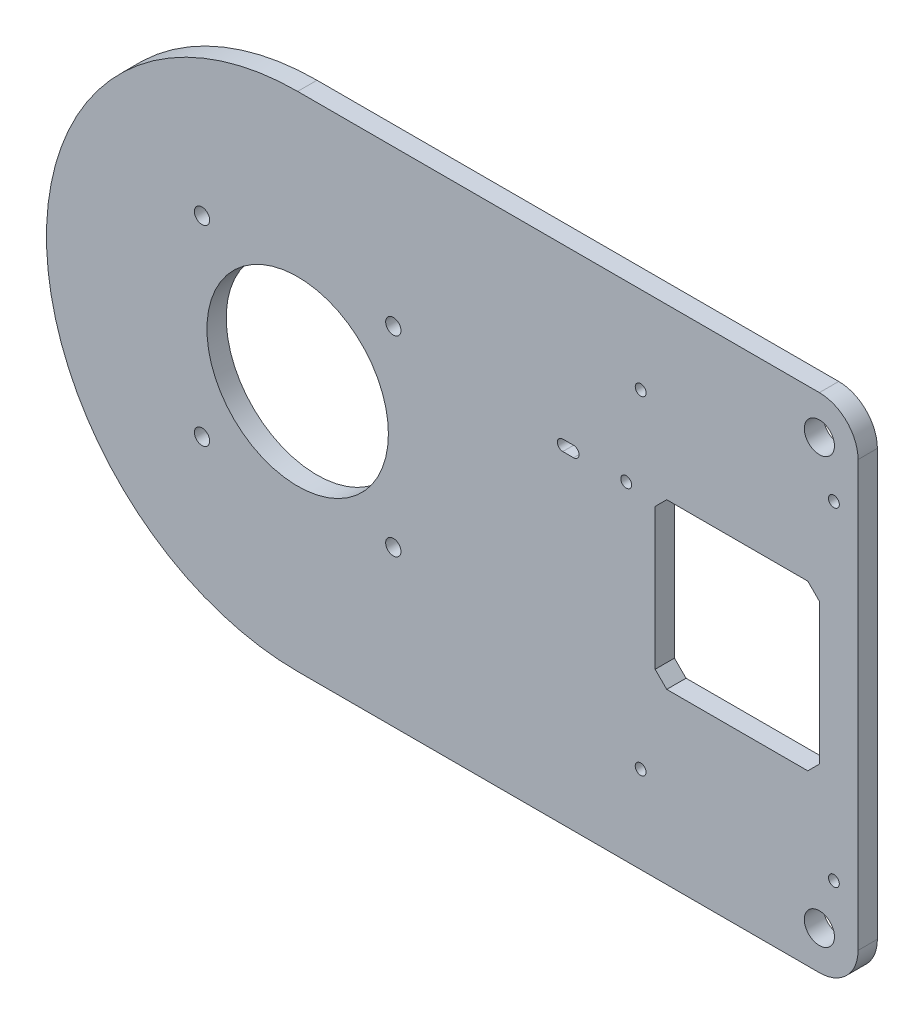
SolidWorks part; units mm, degrees
ref_plane "Front Plane" through (0, 0, 0) normal (0, 0, 1) x (1, 0, 0)
ref_plane "Top Plane" through (0, 0, 0) normal (0, 1, 0) x (1, 0, 0)
ref_plane "Right Plane" through (0, 0, 0) normal (1, 0, 0) x (0, 0, -1)
sketch "Sketch1" plane through (0, 0, 0) normal (0, 0, 1) x (1, 0, 0)
  line L0 (-105, 0) -> (105, 0) construction
  line L3 (-40, -65) -> (95, -65)
  line L4 (105, 55) -> (105, -55)
  line L5 (-40, 65) -> (95, 65)
  line L6 (95, 65) -> (95, -65) construction
  line L7 (-40, 81.3754) -> (-40, -121.1815) construction
  line L8 (95, 18.25) -> (95, -18.25)
  line L9 (92, 21.25) -> (55.5, 21.25)
  line L10 (52.5, 18.25) -> (52.5, -18.25)
  line L11 (55.5, -21.25) -> (92, -21.25)
  line L12 (52.5, -18.25) -> (55.5, -21.25)
  line L13 (92, 21.25) -> (95, 18.25)
  line L14 (55.5, 21.25) -> (52.5, 18.25)
  line L15 (95, -18.25) -> (92, -21.25)
  line L16 (48.75, 42.5) -> (48.75, -42.5) construction
  line L17 (73.75, 21.25) -> (73.75, -21.25) construction
  line L18 (52.5, 0) -> (95, 0) construction
  line L19 (28.6, 20) -> (31.4, 20) construction
  line L20 (28.6, 21.4) -> (31.4, 21.4)
  line L21 (28.6, 18.6) -> (31.4, 18.6)
  circle A0 centre (95, 55) radius 3.9
  circle A1 centre (95, -55) radius 3.9
  arc A2 (-40, 65) -> (-40, -65) centre (-40, 0) ccw
  arc A4 (95, -65) -> (105, -55) centre (95, -55) ccw
  arc A5 (95, 65) -> (105, 55) centre (95, 55) cw
  circle A6 centre (-40, 0) radius 23.48
  circle A7 centre (-64.75, 24.75) radius 1.975
  circle A8 centre (-15.25, 24.75) radius 1.975
  circle A9 centre (-15.25, -24.75) radius 1.975
  circle A10 centre (-64.75, -24.75) radius 1.975
  circle A11 centre (98.75, 42.5) radius 1.4
  circle A13 centre (48.75, 42.5) radius 1.4
  circle A15 centre (48.75, -42.5) radius 1.4
  circle A16 centre (98.75, -42.5) radius 1.4
  circle A17 centre (45, 20) radius 1.4
  arc A21 (28.6, 21.4) -> (28.6, 18.6) centre (28.6, 20) ccw
  arc A22 (31.4, 18.6) -> (31.4, 21.4) centre (31.4, 20) ccw
  point P0 (0, 0)
  point P19 (105, -65)
  point P22 (105, 65)
  point P32 (95, 21.25)
  point P33 (95, -21.25)
  point P36 (52.5, 21.25)
  point P37 (52.5, -21.25)
  point P44 (73.75, 0)
  point P48 (73.75, 0)
  point P60 (30, 20)
  dimension "D3" = 7.8
  dimension "D7" = 65
  dimension "D6" = 40
  dimension "D8" = 21.25
  dimension "D4" = 105
  dimension "D5" = 10
  dimension "D9" = 110
  dimension "D10" = 46.96
  dimension "D11" = 3.95
  dimension "D14" = 42.5
  dimension "D16" = 42.5
  dimension "D19" = 2.8
  dimension "D30" = 2.8
  dimension "D31" = 20
  dimension "D35" = 13.6
  dimension "D34" = 1.4
  dimension "D1" = 65
  dimension "D2" = 65
  dimension "D12" = 24.75
  dimension "D13" = 24.75
  dimension "D15" = 42.5
  dimension "D17" = 4.2426
  dimension "D18" = 4.2426
  dimension "D20" = 4.2426
  dimension "D21" = 4.2426
  dimension "D22" = 36.5
  dimension "D23" = 42.5
  dimension "D28" = 25
  dimension "D29" = 85
  dimension "D32" = 7.5
  dimension "D33" = 2.8
extrude "Boss-Extrude4" add sketch "Sketch1" along normal blind 5
